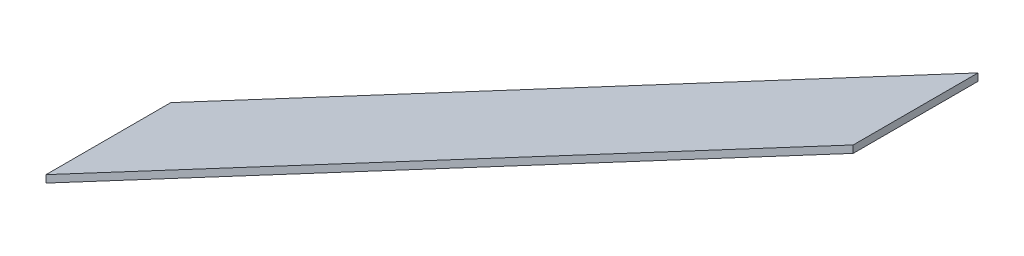
SolidWorks part; units mm, degrees
ref_plane "Front Plane" through (0, 0, 0) normal (0, 0, 1) x (1, 0, 0)
ref_plane "Top Plane" through (0, 0, 0) normal (0, 1, 0) x (1, 0, 0)
ref_plane "Right Plane" through (0, 0, 0) normal (1, 0, 0) x (0, 0, -1)
sketch "Sketch1" plane through (0, 0, 0) normal (0, 0, 1) x (1, 0, 0)
  line L0 (-1000, -50) -> (-6499.448, -2975)
  line L1 (-1000, -50) -> (-1000, 0)
  line L2 (-1000, 0) -> (-6499.448, -2925)
  line L3 (-6499.448, -2925) -> (-6499.448, -2975)
extrude "Extrude1" add sketch "Sketch1" against normal blind 850
